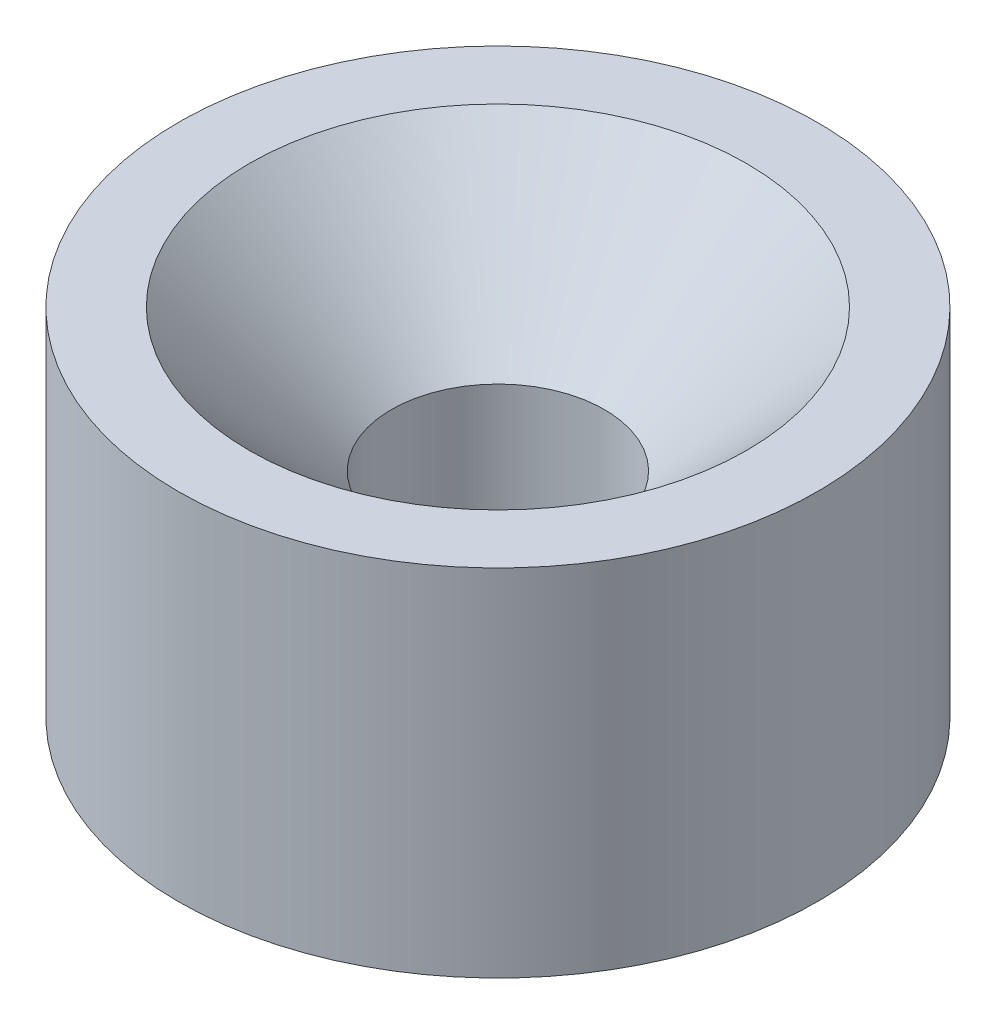
SolidWorks part; units mm, degrees
ref_plane "Front Plane" through (0, 0, 0) normal (0, 0, 1) x (1, 0, 0)
ref_plane "Top Plane" through (0, 0, 0) normal (0, 1, 0) x (1, 0, 0)
ref_plane "Right Plane" through (0, 0, 0) normal (1, 0, 0) x (0, 0, -1)
sketch "Sketch1" plane through (0, 0, 0) normal (0, 1, 0) x (1, 0, 0)
  circle A0 centre (0, 0) radius 4.5
  circle A1 centre (0, 0) radius 1.5
  dimension "D1" = 3
  dimension "D2" = 9
extrude "Boss-Extrude1" add sketch "Sketch1" along normal blind 5
chamfer "Chamfer1" distance 2 angle 45 1 edges at (0, 5, 1.5)
